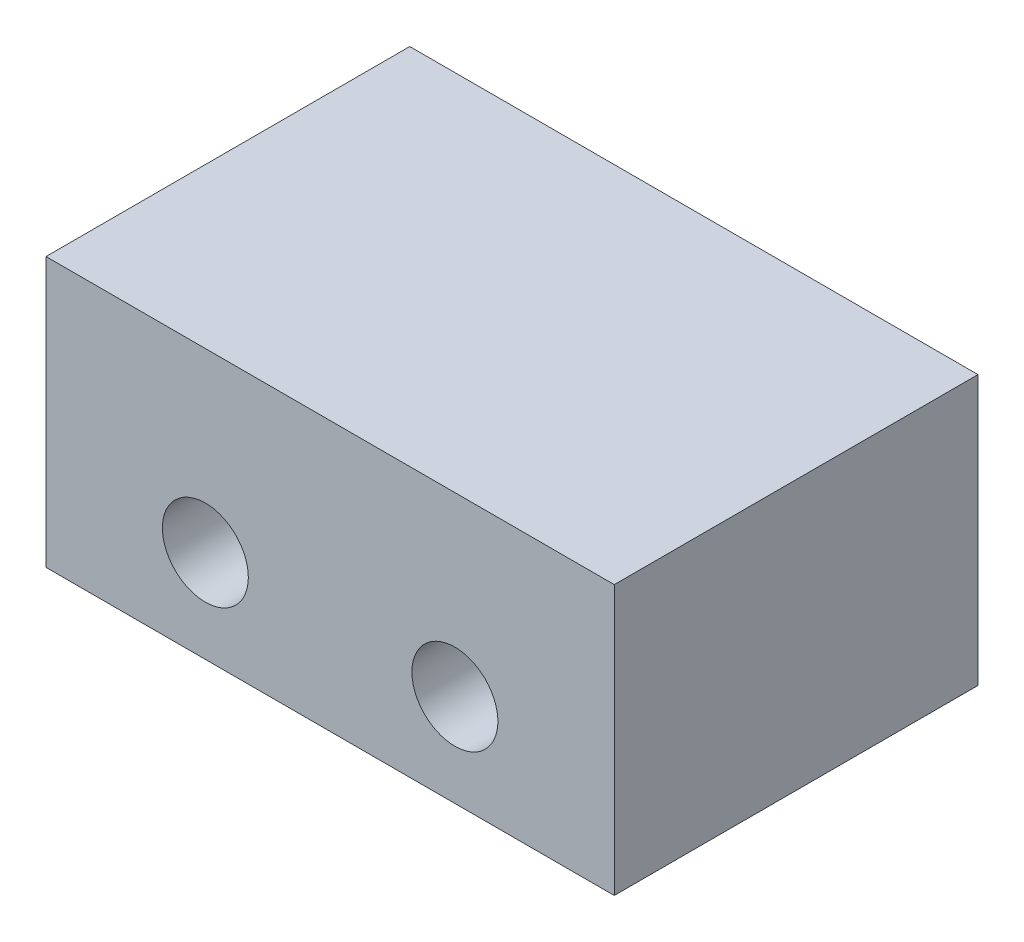
SolidWorks part; units mm, degrees
ref_plane "Front Plane" through (0, 0, 0) normal (0, 0, 1) x (1, 0, 0)
ref_plane "Top Plane" through (0, 0, 0) normal (0, 1, 0) x (1, 0, 0)
ref_plane "Right Plane" through (0, 0, 0) normal (1, 0, 0) x (0, 0, -1)
sketch "Sketch2" plane through (0, 0, 0) normal (0, 0, 1) x (1, 0, 0)
  line L0 (9.92, 9.4) -> (9.92, 0) construction
  line L1 (0, 0) -> (19.84, 0)
  line L2 (0, 0) -> (0, 9.4)
  line L3 (0, 9.4) -> (19.84, 9.4)
  line L4 (19.84, 0) -> (19.84, 9.4)
  line L5 (4.064, 3.23) -> (0, 3.23) construction
  line L6 (5.564, 1.73) -> (5.564, 0) construction
  circle A0 centre (5.564, 3.23) radius 1.5
  circle A1 centre (14.276, 3.23) radius 1.5
  dimension "D5" = 3
  dimension "D1" = 19.84
  dimension "D2" = 9.4
  dimension "D3" = 4.064
  dimension "D4" = 1.73
extrude "Boss-Extrude1" add sketch "Sketch2" along normal blind 12.7
equation "\"depth\"= 7.3"
equation "\"height\"= 9.5"
equation "\"width\"= 8.60"
equation "\"flipWidth\"= 6.5"
equation "\"flipHeight\"= 4"
equation "\"spindleLength\"= 7.75"
equation "\"bearingID\"= 0.1559"
equation "\"bearingOD\"= 0.3539\t"
equation "\"motorWidth\"= 0.79"
equation "\"motorHeight\"= 1.0"
equation "\"motorLength\"= 1.58"
equation "\"spindleMaxDiam\"= 2.75"
equation "\"totalLength\"= 15"
equation "\"stopperWidth\"= 0.13"
equation "\"stopperHeight\"= 0.31"
equation "\"stopperLength\"= 8.73"
